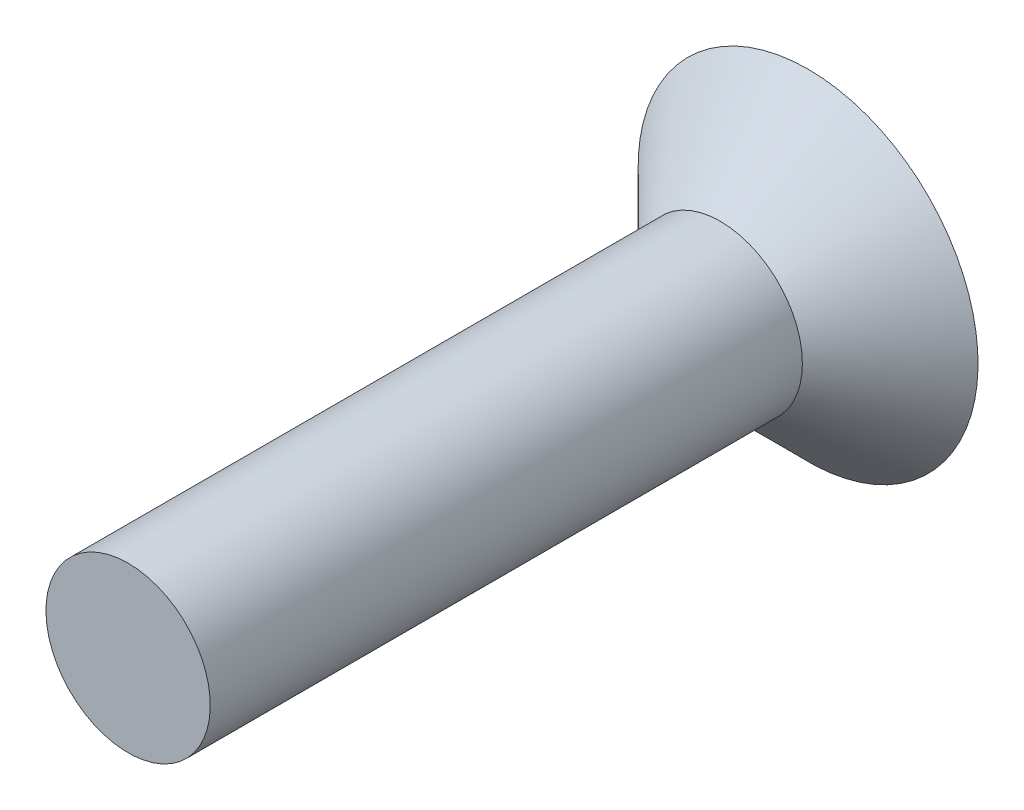
SolidWorks part; units mm, degrees
ref_plane "Front Plane" through (0, 0, 0) normal (0, 0, 1) x (1, 0, 0)
ref_plane "Top Plane" through (0, 0, 0) normal (0, 1, 0) x (1, 0, 0)
ref_plane "Right Plane" through (0, 0, 0) normal (1, 0, 0) x (0, 0, -1)
sketch "Sketch3" plane through (0, 0, 0) normal (1, 0, 0) x (0, 0, -1)
  line L0 (0, 3) -> (-1.55, 1.45)
  line L1 (0, 0) -> (-1.55, 0)
  line L2 (-1.55, 1.45) -> (-1.55, 0)
  line L4 (0, 0) -> (0, 3)
  point P2 (-0.4, 2.6)
  point P8 (-1, 1)
  dimension "D1" = 1.45
  dimension "D2" = 45
  dimension "D3" = 3
  dimension "D4" = 2.6
revolve "Revolve1" add sketch "Sketch3" angle 360 about L1
sketch "Sketch5" plane through (0, 0, 1.55) normal (0, 0, 1) x (1, 0, 0)
  circle A0 centre (0, 0) radius 1.45
extrude "Boss-Extrude1" add sketch "Sketch5" along normal blind 12 from surface at -1.55 starting at face at (0, 3, 0)
ref_plane "Plane1" through (0, 0, 0.4) normal (0, 0, 1) x (1, 0, 0)
sketch "Sketch7" plane through (0, 0, 0.4) normal (0, 0, 1) x (1, 0, 0)
  circle A0 centre (0, 0) radius 1.55
  circle A1 centre (0, 0) radius 0.95
  dimension "D1" = 3.1
  dimension "D2" = 1.9
equation "\"D4@Sketch3\"=5.2/2"
equation "\"D1@Sketch3\"=2.9/2"
